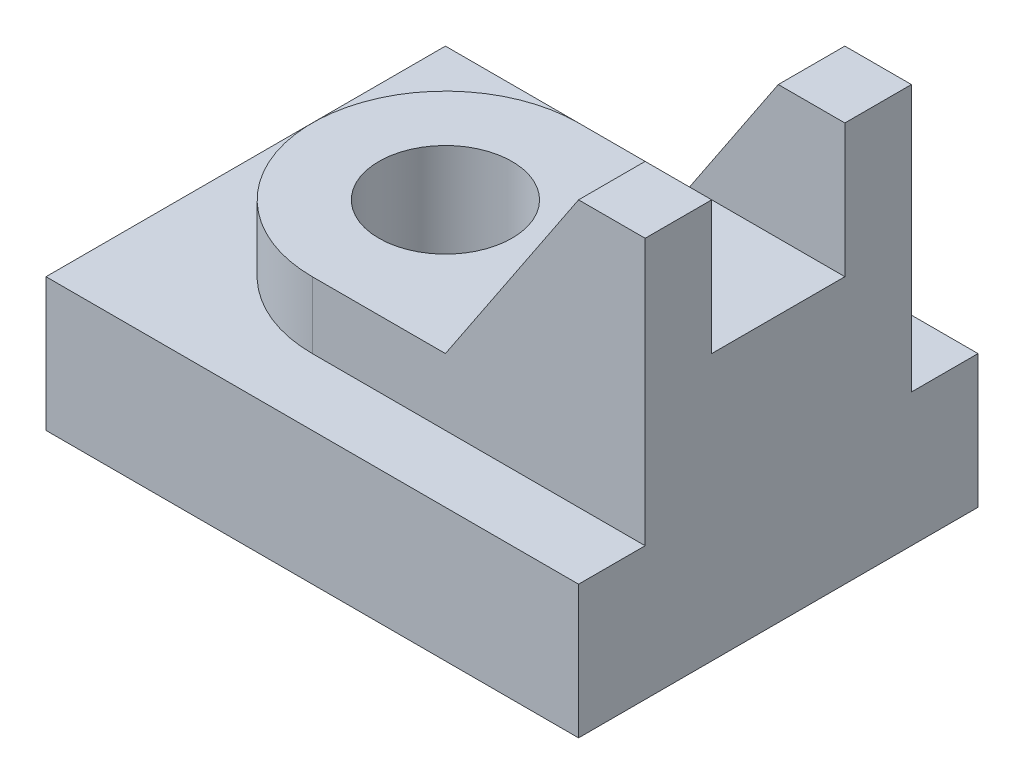
SolidWorks part; units mm, degrees
material "Ferro fundido maleável"
ref_plane "Plano frontal" through (0, 0, 0) normal (0, 0, 1) x (1, 0, 0)
ref_plane "Plano superior" through (0, 0, 0) normal (0, 1, 0) x (1, 0, 0)
ref_plane "Plano direito" through (0, 0, 0) normal (1, 0, 0) x (0, 0, -1)
sketch "Esboço1" plane through (0, 0, 0) normal (0, 1, 0) x (1, 0, 0)
  line L1 (-20, -15) -> (20, -15)
  line L2 (-20, -15) -> (-20, 15)
  line L3 (-20, 15) -> (20, 15)
  line L4 (20, -15) -> (20, 15)
  line L5 (-20, -15) -> (20, 15) construction
  line L6 (-20, 15) -> (20, -15) construction
  point P0 (0, 0)
  dimension "D1" = 40
  dimension "D2" = 30
extrude "Ressalto-extrusão1" add sketch "Esboço1" along normal blind 10
sketch "Esboço2" plane through (0, 10, 0) normal (0, 1, 0) x (1, 0, 0)
  line L0 (20, 10) -> (20, -10)
  line L1 (20, -15) -> (20, 15) construction
  line L2 (20, -10) -> (-5, -10)
  line L3 (20, 10) -> (-5, 10)
  arc A0 (-5, 10) -> (-5, -10) centre (-5, 0) ccw
  point P7 (0, 0)
  point P8 (20, 0)
  dimension "D1" = 25
  dimension "D2" = 20
extrude "Ressalto-extrusão2" add sketch "Esboço2" along normal blind 5
sketch "Esboço3" plane through (0, 0, 10) normal (0, 0, 1) x (1, 0, 0)
  line L0 (20, 15) -> (5, 15)
  line L1 (-5, 15) -> (20, 15) construction
  line L2 (5, 15) -> (15, 30)
  line L3 (15, 30) -> (20, 30)
  line L4 (20, 30) -> (20, 15)
  line L5 (-20, 0) -> (20, 0) construction
  dimension "D1" = 30
  dimension "D2" = 5
  dimension "D3" = 15
extrude "Ressalto-extrusão3" add sketch "Esboço3" against normal up to surface (20 mm away) up to face at (7.5, 12.5, -10)
sketch "Esboço4" plane through (20, 0, 0) normal (1, 0, 0) x (0, 0, -1)
  line L0 (-5, 30) -> (-5, 20)
  line L1 (10, 30) -> (-10, 30) construction
  line L2 (-5, 20) -> (5, 20)
  line L3 (5, 20) -> (5, 30)
  line L4 (5, 30) -> (-5, 30)
  point P6 (0, 30)
  dimension "D1" = 10
extrude "Corte-extrusão1" cut sketch "Esboço4" against normal through all
sketch "Esboço5" plane through (0, 15, 0) normal (0, 1, 0) x (1, 0, 0)
  circle A0 centre (-5, 0) radius 5
  arc A1 (-5, 10) -> (-5, -10) centre (-5, 0) ccw construction
  dimension "D1" = 10
extrude "Corte-extrusão2" cut sketch "Esboço5" against normal through all
